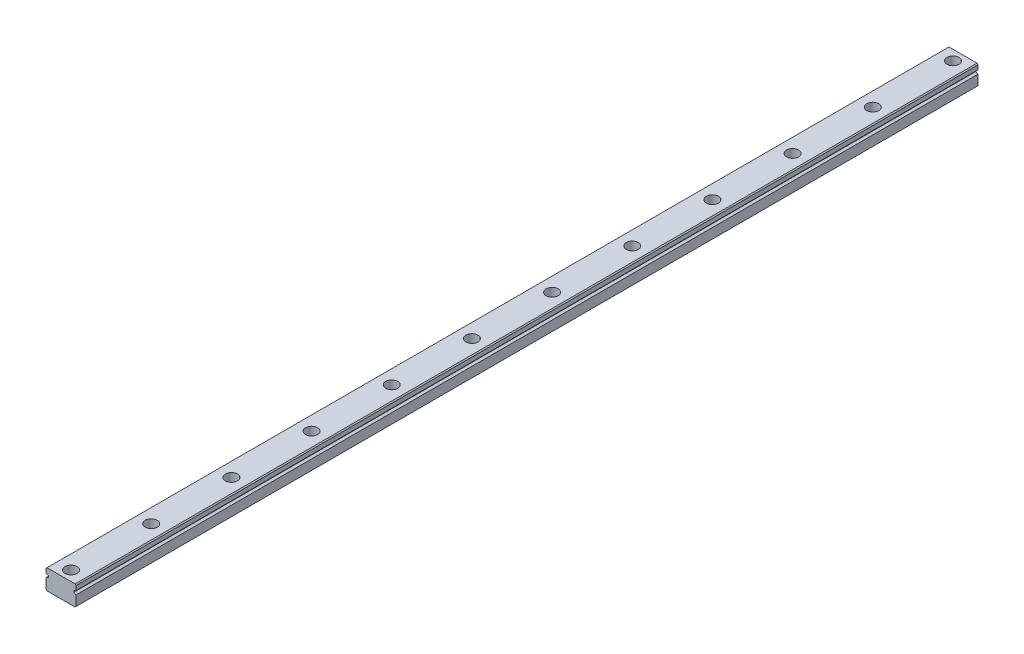
SolidWorks part; units mm, degrees
ref_plane "前视基准面" through (0, 0, 0) normal (0, 0, 1) x (1, 0, 0)
ref_plane "上视基准面" through (0, 0, 0) normal (0, 1, 0) x (1, 0, 0)
ref_plane "右视基准面" through (0, 0, 0) normal (1, 0, 0) x (0, 0, -1)
sketch "草图1" plane through (0, 0, 0) normal (0, 0, 1) x (1, 0, 0)
  line L1 (-3.269, 4.9492) -> (10.731, 4.9492)
  line L2 (-3.769, 4.4492) -> (-3.769, 2.3175)
  line L3 (-3.269, -5.0508) -> (10.731, -5.0508)
  line L4 (11.231, 4.4492) -> (11.231, 2.3175)
  line L6 (11.231, 0.4492) -> (10.0868, 0.9834)
  line L7 (10.0868, 0.9834) -> (10.0868, 1.7834)
  line L8 (-3.769, 0.4492) -> (-2.6248, 0.9834)
  line L9 (11.231, 2.3175) -> (10.0868, 1.7834)
  line L10 (-2.6248, 0.9834) -> (-2.6248, 1.7834)
  line L11 (-3.769, 2.3175) -> (-2.6248, 1.7834)
  line L12 (-3.769, 0.4492) -> (-3.769, -4.5508)
  line L13 (11.231, 0.4492) -> (11.231, -4.5508)
  line L14 (-3.769, 4.4492) -> (-3.269, 4.9492)
  line L15 (10.731, 4.9492) -> (11.231, 4.4492)
  line L16 (11.231, -4.5508) -> (10.731, -5.0508)
  line L17 (-3.769, -4.5508) -> (-3.269, -5.0508)
  point P0 (-3.769, 4.9492)
  point P1 (11.231, -5.0508)
  point P2 (-3.769, -5.0508)
  point P3 (11.231, 4.9492)
  point P15 (10.0868, 1.3834)
  dimension "D1" = 15
  dimension "D2" = 10
extrude "凸台-拉伸1" add sketch "草图1" against normal blind 450
ref_plane "基准面4" through (10.731, 4.9492, 0) normal (0, 0, 1) x (1, 0, 0)
sketch "草图2" plane through (0, 4.9492, 0) normal (0, 1, 0) x (1, 0, 0)
  line L0 (3.731, 450) -> (3.731, 0)
  line L1 (10.731, 450) -> (-3.269, 450) construction
  line L2 (10.731, 0) -> (-3.269, 0) construction
  line L3 (3.731, 225) -> (39.9645, 225)
  line L4 (34.2494, 205) -> (-14.6467, 205)
  line L5 (34.2494, 165) -> (-14.6467, 165)
  line L6 (34.2494, 125) -> (-14.6467, 125)
  line L7 (34.2494, 85) -> (-14.6467, 85)
  line L8 (34.2494, 45) -> (-14.6467, 45)
  line L9 (31.5707, 5) -> (-14.6467, 5)
  line L10 (31.5707, 445) -> (-14.6467, 445)
  line L11 (34.2494, 405) -> (-14.6467, 405)
  line L12 (34.2494, 365) -> (-14.6467, 365)
  line L13 (34.2494, 325) -> (-14.6467, 325)
  line L14 (34.2494, 285) -> (-14.6467, 285)
  line L15 (34.2494, 245) -> (-14.6467, 245)
  dimension "D1" = 20
  dimension "D2" = 40
  dimension "D3" = 40
  dimension "D4" = 40
  dimension "D5" = 40
  dimension "D6" = 40
hole_wizard "孔1" positions "3D草图1" profile "草图3" legacy end condition through all
sketch3d "3D草图1"
  line L0 (3.731, 4.9492, -450) -> (3.731, 4.9492, 0) construction
  line L1 (31.5707, 4.9492, -445) -> (-14.6467, 4.9492, -445) construction
  line L2 (34.2494, 4.9492, -405) -> (-14.6467, 4.9492, -405) construction
  line L3 (34.2494, 4.9492, -365) -> (-14.6467, 4.9492, -365) construction
  line L4 (34.2494, 4.9492, -325) -> (-14.6467, 4.9492, -325) construction
  line L5 (34.2494, 4.9492, -285) -> (-14.6467, 4.9492, -285) construction
  line L6 (34.2494, 4.9492, -245) -> (-14.6467, 4.9492, -245) construction
  line L7 (34.2494, 4.9492, -205) -> (-14.6467, 4.9492, -205) construction
  line L8 (34.2494, 4.9492, -165) -> (-14.6467, 4.9492, -165) construction
  line L9 (34.2494, 4.9492, -125) -> (-14.6467, 4.9492, -125) construction
  line L10 (34.2494, 4.9492, -85) -> (-14.6467, 4.9492, -85) construction
  line L11 (34.2494, 4.9492, -45) -> (-14.6467, 4.9492, -45) construction
  line L12 (31.5707, 4.9492, -5) -> (-14.6467, 4.9492, -5) construction
  point P0 (3.731, 4.9492, -445)
  point P6 (3.731, 4.9492, -405)
  point P10 (3.731, 4.9492, -365)
  point P14 (3.731, 4.9492, -325)
  point P18 (3.731, 4.9492, -285)
  point P22 (3.731, 4.9492, -245)
  point P26 (3.731, 4.9492, -205)
  point P30 (3.731, 4.9492, -165)
  point P34 (3.731, 4.9492, -125)
  point P38 (3.731, 4.9492, -85)
  point P42 (3.731, 4.9492, -45)
  point P46 (3.731, 4.9492, -5)
sketch "草图3" plane through (3.731, 4.9492, -445) normal (1, 0, 0) x (0, 0, 1)
  line L0 (0, 0) -> (0, 10)
  line L1 (0, 10) -> (1.6, 10)
  line L2 (1.6, 10) -> (1.6, 4.5)
  line L3 (1.6, 4.5) -> (3, 4.5)
  line L4 (3, 4.5) -> (3, 0)
  line L5 (3, 0) -> (0, 0)
  line L6 (0, 110) -> (0, -10) construction
  dimension "直径" = 3.2
  dimension "深度" = 10
  dimension "柱坑直径" = 6
  dimension "柱坑深度" = 4.5
